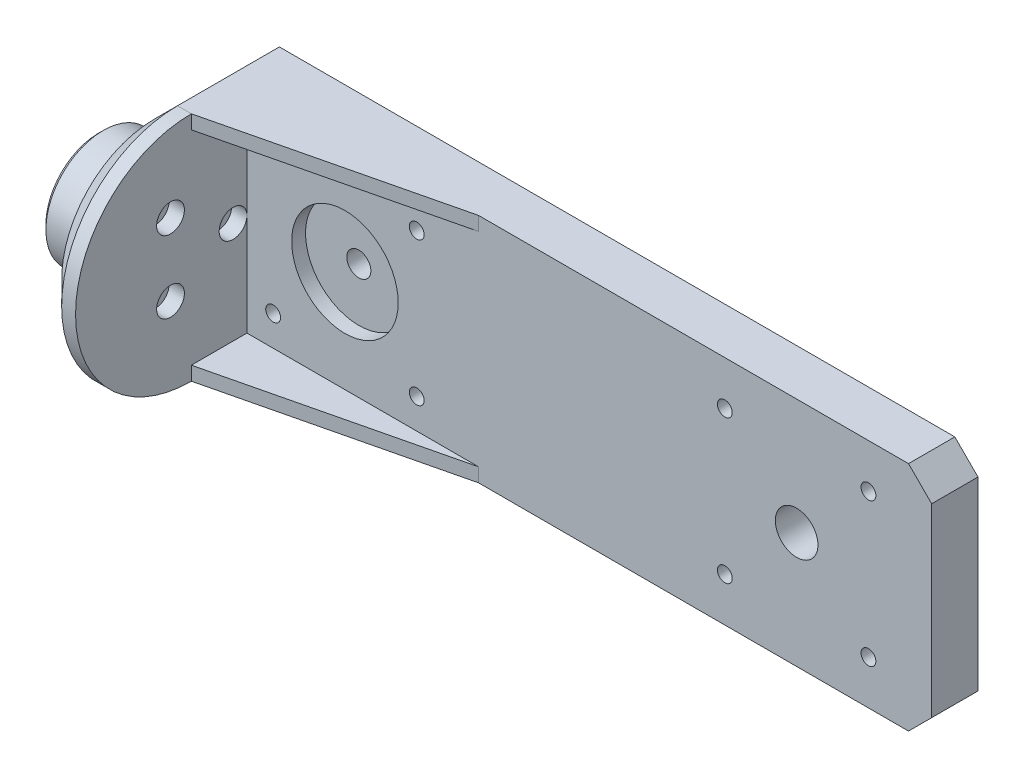
SolidWorks part; units mm, degrees
ref_plane "前视基准面" through (0, 0, 0) normal (0, 0, 1) x (1, 0, 0)
ref_plane "上视基准面" through (0, 0, 0) normal (0, 1, 0) x (1, 0, 0)
ref_plane "右视基准面" through (0, 0, 0) normal (1, 0, 0) x (0, 0, -1)
other "Configuration Table"
sketch "草图2" plane through (0, 0, 0) normal (1, 0, 0) x (0, 0, -1)
  line L0 (0, 0) -> (9, 0) construction
  line L1 (0, 0) -> (-4.5, -7.7942) construction
  circle A0 centre (0, 0) radius 12.4
  circle A1 centre (9, 0) radius 1.6
  circle A2 centre (-4.5, -7.7942) radius 1.6
  circle A3 centre (-4.5, 7.7942) radius 1.6
  dimension "D1" = 24.8
  dimension "D2" = 9
  dimension "D3" = 3.2
  dimension "D5" = 120
  dimension "D4" = 3
extrude "凸台-拉伸1" add sketch "草图2" along normal blind 20
sketch "草图3" plane through (20, 0, 0) normal (1, 0, 0) x (0, 0, -1)
  line L3 (0, 25) -> (12, 25)
  line L4 (12, 25) -> (12, -25)
  line L5 (12, -25) -> (0, -25)
  arc A2 (0, 25) -> (0, -25) centre (0, 0) ccw
  arc A3 (12, 3.1241) -> (12, -3.1241) centre (0, 0) ccw
  circle M6 centre (0, 0) radius 12.4
  dimension "D2" = 50
  dimension "D1" = 24.8
  dimension "D3" = 12
extrude "凸台-拉伸2" add sketch "草图3" against normal blind 8 contours L3 A2 L5 L4 M6
sketch "草图5" plane through (0, 0, -12) normal (0, 0, -1) x (-1, 0, 0)
  line L1 (-12, -25) -> (-167.81, -25)
  line L2 (-12, -25) -> (-12, 25)
  line L3 (-12, 25) -> (-167.81, 25)
  line L8 (-167.81, 25) -> (-167.81, -25)
  line L9 (-12, -3.1241) -> (-12, -25) construction
  dimension "D1" = 155.81
extrude "凸台-拉伸3" add sketch "草图5" along normal blind 10
sketch "草图6" plane through (0, 0, -12) normal (0, 0, 1) x (1, 0, 0)
  line L1 (20, 0) -> (158.66, 0) construction
  line L2 (20, -25) -> (20, 25) construction
  line L3 (25.65, 15.5) -> (56.65, 15.5) construction
  line L4 (25.65, 15.5) -> (25.65, -15.5) construction
  line L5 (25.65, -15.5) -> (56.65, 15.5) construction
  line L7 (25.65, 15.5) -> (123.16, 15.5) construction
  circle A0 centre (25.65, 15.5) radius 1.6
  circle A2 centre (56.65, 15.5) radius 1.6
  circle A3 centre (56.65, -15.5) radius 1.6
  circle A4 centre (25.65, -15.5) radius 1.6
  circle A5 centre (41.15, 0) radius 2.6
  circle A6 centre (138.66, 0) radius 4.6
  circle A7 centre (123.16, 15.5) radius 1.6
  circle A8 centre (154.16, 15.5) radius 1.6
  circle A9 centre (154.16, -15.5) radius 1.6
  circle A10 centre (123.16, -15.5) radius 1.6
  dimension "D6" = 15.5
  dimension "D7" = 5.65
  dimension "D8" = 3.2
  dimension "D9" = 5.2
  dimension "D10" = 9.2
  dimension "D11" = 97.51
  dimension "D1" = 2
  dimension "D3" = 90
  dimension "D4" = 31
  dimension "D5" = 31
  dimension "D13" = 97.51
  dimension "D2" = 2
  dimension "D12" = 2
extrude "切除-拉伸1" cut sketch "草图6" against normal blind 10
sketch "草图7" plane through (20, 0, 0) normal (1, 0, 0) x (0, 0, -1)
  circle A0 centre (-4.5, 7.7942) radius 3
  circle A1 centre (9, 0) radius 3
  circle A2 centre (-4.5, -7.7942) radius 3
  dimension "D1" = 6
extrude "切除-拉伸2" cut sketch "草图7" against normal blind 3.3
sketch "草图8" plane through (0, 0, -12) normal (0, 0, 1) x (1, 0, 0)
  circle A0 centre (41.15, 0) radius 11.5
  dimension "D1" = 23
extrude "切除-拉伸3" cut sketch "草图8" against normal blind 3
sketch "草图10" plane through (0, -25, 0) normal (0, -1, 0) x (1, 0, 0)
  line L0 (20, 0) -> (70, -12)
  line L2 (167.81, -12) -> (20, -12) construction
  line L3 (70, -12) -> (20, -12)
  line L4 (20, -12) -> (20, 0)
  line L5 (20, 0) -> (20, 25) construction
  line L6 (20, -12) -> (20, 0) construction
  dimension "D2" = 50
extrude "凸台-拉伸4" add sketch "草图10" against normal blind 3
sketch "草图11" plane through (0, 25, 0) normal (0, 1, 0) x (1, 0, 0)
  line L3 (20, 12) -> (20, 0)
  line L4 (20, 0) -> (70, 12)
  line L7 (20, 0) -> (70, 12)
  line L12 (20, 12) -> (20, 0)
  line L13 (70, 12) -> (20, 12)
  line L14 (70, 12) -> (20, 12)
  dimension "D1" = 0
extrude "凸台-拉伸5" add sketch "草图11" against normal blind 3
chamfer "倒角1" distance 5 angle 45 5 edges at (167.81, -25, -17) (167.81, 25, -17) (12, -25, -11) (12, 0, 25) (12, 25, -11)
chamfer "倒角2" distance 1 angle 45 1 edges at (0, 0, -12.4)
